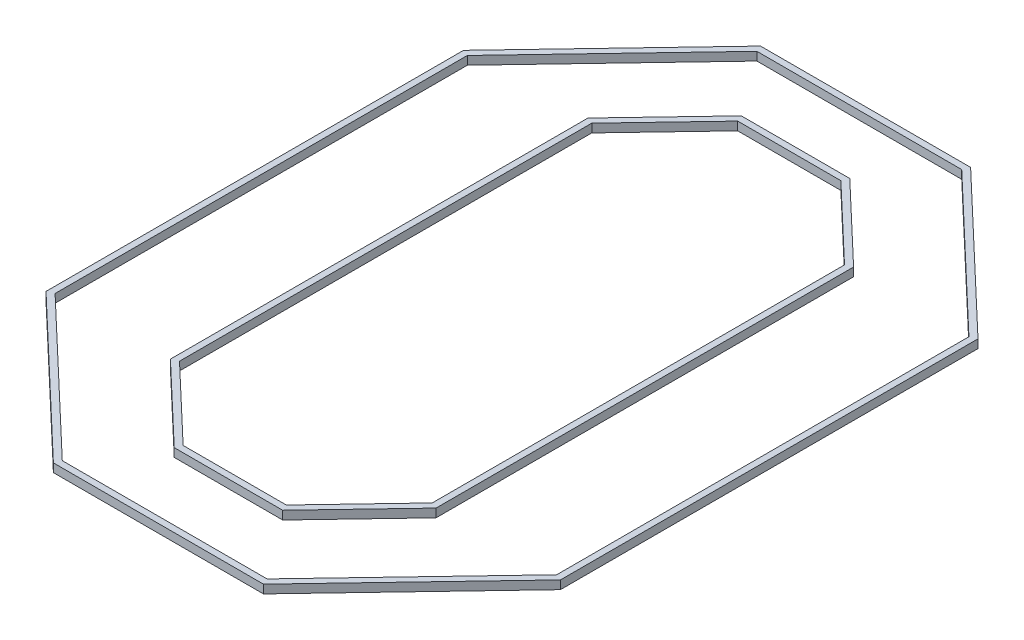
SolidWorks part; units mm, degrees
ref_plane "Front Plane" through (0, 0, 0) normal (0, 0, 1) x (1, 0, 0)
ref_plane "Top Plane" through (0, 0, 0) normal (0, 1, 0) x (1, 0, 0)
ref_plane "Right Plane" through (0, 0, 0) normal (1, 0, 0) x (0, 0, -1)
sketch "Sketch1" plane through (0, 0, 0) normal (0, 1, 0) x (1, 0, 0)
  line L0 (3048, 2489.2) -> (3048, 0) construction
  line L1 (3048, 0) -> (3048, -2489.2) construction
  line L2 (-1244.6, 4204.9695) -> (1244.6, 4204.9695) construction
  line L3 (1244.6, 4204.9695) -> (3048, 2489.2) construction
  line L4 (1555.102, 2489.2) -> (1555.102, 0) construction
  line L5 (1555.102, 2489.2) -> (635, 3364.5926) construction
  line L6 (1555.102, 0) -> (1555.102, -2489.2) construction
  line L7 (1555.102, -2489.2) -> (679.7094, -3409.302) construction
  line L8 (3048, -2489.2) -> (1332.2305, -4292.6) construction
  line L9 (1332.2305, -4292.6) -> (-1156.9695, -4292.6) construction
  line L10 (635, 3364.5926) -> (-635, 3364.5926) construction
  line L11 (679.7094, -3409.302) -> (-590.2906, -3409.302) construction
  line L12 (-590.2906, -3409.302) -> (-1510.3926, -2533.9094) construction
  line L13 (-635, 3364.5926) -> (-1510.3926, 2444.4906) construction
  line L14 (-1510.3926, 2444.4906) -> (-1510.3926, -44.7094) construction
  line L15 (-1510.3926, -44.7094) -> (-1510.3926, -2533.9094) construction
  line L16 (-1156.9695, -4292.6) -> (-2960.3695, -2576.8305) construction
  line L17 (-2960.3695, -2576.8305) -> (-2960.3695, -87.6305) construction
  line L18 (-2960.3695, -87.6305) -> (-2960.3695, 2401.5695) construction
  line L19 (-2960.3695, 2401.5695) -> (-1244.6, 4204.9695) construction
  line L20 (-2998.4695, -87.6305) -> (-2998.4695, 2416.7983)
  line L21 (-2998.4695, 2416.7983) -> (-1260.9401, 4243.0695)
  line L22 (-1260.9401, 4243.0695) -> (1259.8287, 4243.0695)
  line L23 (1259.8287, 4243.0695) -> (3086.1, 2505.5401)
  line L24 (3086.1, 2505.5401) -> (3086.1, 0)
  line L25 (3086.1, 0) -> (3086.1, -2504.4287)
  line L26 (3086.1, -2504.4287) -> (1348.5706, -4330.7)
  line L27 (1348.5706, -4330.7) -> (-1172.1983, -4330.7)
  line L28 (-1172.1983, -4330.7) -> (-2998.4695, -2593.1706)
  line L29 (-2998.4695, -2593.1706) -> (-2998.4695, -87.6305)
  line L30 (-2922.2695, -87.6305) -> (-2922.2695, 2386.3408)
  line L31 (-2922.2695, 2386.3408) -> (-1228.2599, 4166.8695)
  line L32 (-1228.2599, 4166.8695) -> (1229.3713, 4166.8695)
  line L33 (1229.3713, 4166.8695) -> (3009.9, 2472.8599)
  line L34 (3009.9, 2472.8599) -> (3009.9, 0)
  line L35 (3009.9, 0) -> (3009.9, -2473.9713)
  line L36 (3009.9, -2473.9713) -> (1315.8904, -4254.5)
  line L37 (1315.8904, -4254.5) -> (-1141.7408, -4254.5)
  line L38 (-1141.7408, -4254.5) -> (-2922.2695, -2560.4904)
  line L39 (-2922.2695, -2560.4904) -> (-2922.2695, -87.6305)
  line L40 (-1548.4926, -44.7094) -> (-1548.4926, -2550.2495)
  line L41 (-605.5193, -3447.402) -> (-1548.4926, -2550.2495)
  line L42 (696.0495, -3447.402) -> (-605.5193, -3447.402)
  line L43 (1593.202, -2504.4287) -> (696.0495, -3447.402)
  line L44 (1593.202, 0) -> (1593.202, -2504.4287)
  line L45 (1593.202, 2505.5401) -> (1593.202, 0)
  line L46 (1593.202, 2505.5401) -> (650.2287, 3402.6926)
  line L47 (650.2287, 3402.6926) -> (-651.3401, 3402.6926)
  line L48 (-651.3401, 3402.6926) -> (-1548.4926, 2459.7193)
  line L49 (-1548.4926, 2459.7193) -> (-1548.4926, -44.7094)
  line L50 (-1472.2926, -44.7094) -> (-1472.2926, -2517.5693)
  line L51 (-575.0619, -3371.202) -> (-1472.2926, -2517.5693)
  line L52 (663.3693, -3371.202) -> (-575.0619, -3371.202)
  line L53 (1517.002, -2473.9713) -> (663.3693, -3371.202)
  line L54 (1517.002, 0) -> (1517.002, -2473.9713)
  line L55 (1517.002, 2472.8599) -> (1517.002, 0)
  line L56 (1517.002, 2472.8599) -> (619.7713, 3326.4926)
  line L57 (619.7713, 3326.4926) -> (-618.6599, 3326.4926)
  line L58 (-618.6599, 3326.4926) -> (-1472.2926, 2429.2619)
  line L59 (-1472.2926, 2429.2619) -> (-1472.2926, -44.7094)
  point P6 (0, 4204.9695)
  point P8 (0, 3364.5926)
  dimension "D1" = 3048
  dimension "D2" = 2489.2
  dimension "D3" = 0
  dimension "D4" = 1270
  dimension "D5" = 0
  dimension "D6" = 0
  dimension "D7" = 38.1
  dimension "D8" = 38.1
  dimension "D9" = 38.1
  dimension "D10" = 38.1
extrude "Boss-Extrude1" add sketch "Sketch1" along normal blind 101.6 contours L29 L28 L27 L26 L25 L24 L23 L22 L21 L20 L38 L39 L30 L31 L32 L33 L34 L35 L36 L37 | L48 L49 L40 L41 L42 L43 L44 L45 L46 L47 L59 L58 L57 L56 L55 L54 L53 L52 L51 L50
